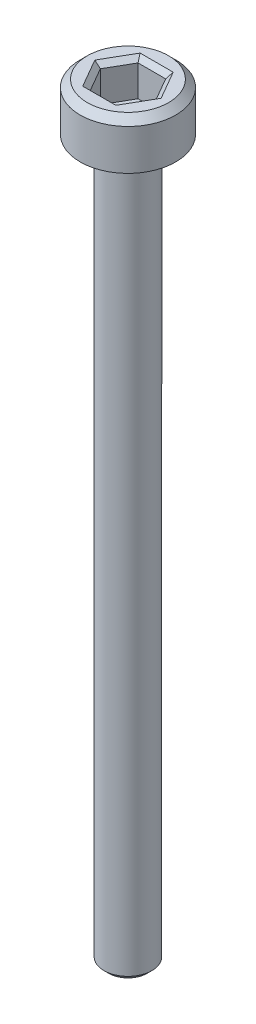
SolidWorks part; units mm, degrees
ref_plane "Front Plane" through (0, 0, 0) normal (0, 0, 1) x (1, 0, 0)
ref_plane "Top Plane" through (0, 0, 0) normal (0, 1, 0) x (1, 0, 0)
ref_plane "Right Plane" through (0, 0, 0) normal (1, 0, 0) x (0, 0, -1)
sketch "Sketch1" plane through (0, 0, 0) normal (0, 1, 0) x (1, 0, 0)
  circle A0 centre (0, 0) radius 2
  dimension "D1" = 4
extrude "Boss-Extrude1" add sketch "Sketch1" along normal blind 2
chamfer "Chamfer1" distance 0.3 angle 45 1 edges at (0, 2, 2)
sketch "Sketch2" plane through (0, 2, 0) normal (0, 1, 0) x (1, 0, 0)
  line L1 (1.1547, 0) -> (0.5774, 1)
  line L2 (0.5774, 1) -> (-0.5774, 1)
  line L3 (-0.5774, 1) -> (-1.1547, 0)
  line L4 (-1.1547, 0) -> (-0.5774, -1)
  line L5 (-0.5774, -1) -> (0.5774, -1)
  line L6 (0.5774, -1) -> (1.1547, 0)
  circle A0 centre (0, 0) radius 1 construction
  dimension "D1" = 2
extrude "Cut-Extrude1" cut sketch "Sketch2" against normal blind 1.5
chamfer "Chamfer2" distance 0.2 angle 45 6 edges at (0.866, 2, -0.5) (0.866, 2, 0.5) (0, 2, 1) (-0.866, 2, 0.5) (-0.866, 2, -0.5) (0, 2, -1)
sketch "Sketch3" plane through (0, 0, 0) normal (0, -1, 0) x (1, 0, 0)
  circle A0 centre (0, 0) radius 1
  dimension "D1" = 2
extrude "Boss-Extrude2" add sketch "Sketch3" along normal blind 30
chamfer "Chamfer3" distance 0.2 angle 45 1 edges at (0, -30, -1)
